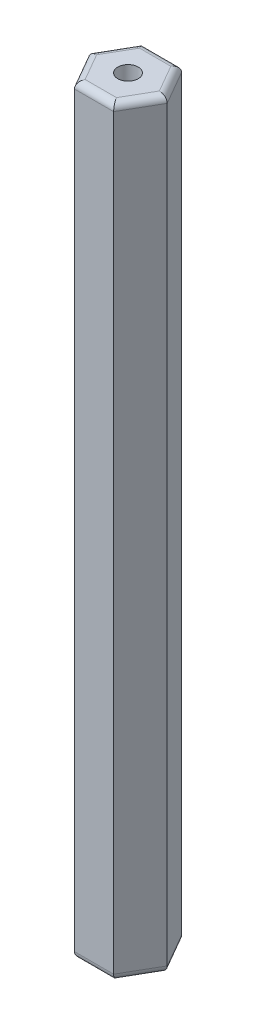
SolidWorks part; units mm, degrees
material "Inox rev"
ref_plane "Plano frontal" through (0, 0, 0) normal (0, 0, 1) x (1, 0, 0)
ref_plane "Plano superior" through (0, 0, 0) normal (0, 1, 0) x (1, 0, 0)
ref_plane "Plano direito" through (0, 0, 0) normal (1, 0, 0) x (0, 0, -1)
ref_plane "Plano1" through (0, -30, 0) normal (0, -1, 0) x (1, 0, 0)
sketch "Esboço1" plane through (0, -30, 0) normal (0, -1, 0) x (1, 0, 0)
  line L0 (-1.4434, -2.5) -> (1.4434, -2.5)
  line L1 (1.4434, -2.5) -> (2.8868, 0)
  line L2 (2.8868, 0) -> (1.4434, 2.5)
  line L3 (1.4434, 2.5) -> (-1.4434, 2.5)
  line L4 (-1.4434, 2.5) -> (-2.8868, 0)
  line L5 (-2.8868, 0) -> (-1.4434, -2.5)
  line L6 (0, 2.5) -> (0, -2.5) construction
  circle A0 centre (0, 0) radius 2.8868 construction
  dimension "D1" = 5
extrude "Ressalto-extrusão1" add sketch "Esboço1" against normal blind 56
fillet "Filete1" radius 0.5 12 edges at (0, -30, 2.5) (2.1651, -30, 1.25) (-2.1651, -30, 1.25) (2.1651, -30, -1.25) (-2.1651, -30, -1.25) (0, -30, -2.5) (0, 26, 2.5) (2.1651, 26, 1.25) (-2.1651, 26, 1.25) (2.1651, 26, -1.25) (-2.1651, 26, -1.25) (0, 26, -2.5)
sketch "Esboço2" plane through (0, -30, 0) normal (0, -1, 0) x (1, 0, 0)
  circle A0 centre (0, 0) radius 0.7514
extrude "Corte-extrusão1" cut sketch "Esboço2" against normal through all
